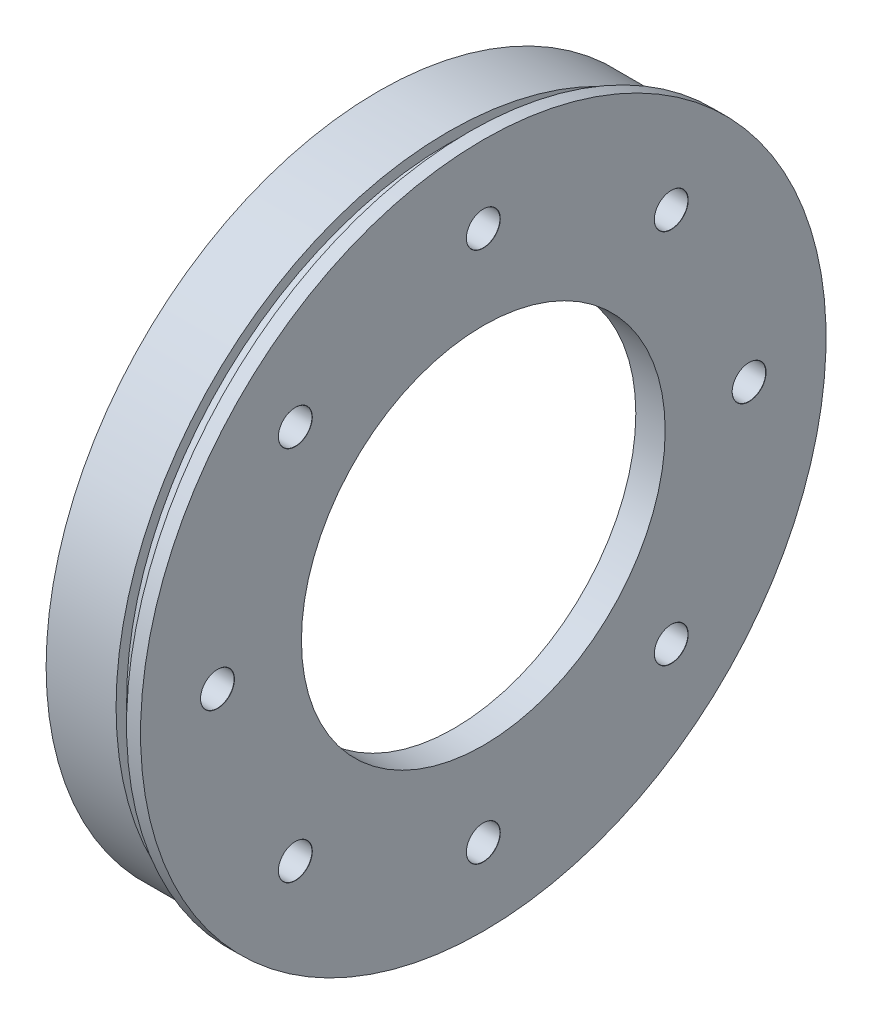
SolidWorks part; units mm, degrees
material "1.4305 (X8CrNiS18-9)"
ref_plane "Ebene vorne" through (0, 0, 0) normal (0, 0, 1) x (1, 0, 0)
ref_plane "Ebene oben" through (0, 0, 0) normal (0, 1, 0) x (1, 0, 0)
ref_plane "Ebene rechts" through (0, 0, 0) normal (1, 0, 0) x (0, 0, -1)
sketch "Sketch1" plane through (0, 0, 0) normal (0, 0, 1) x (1, 0, 0)
  line L0 (0, 0) -> (-24.3345, 0) construction
  line L1 (-15, 47.5) -> (-5, 47.5)
  line L2 (-5, 47.5) -> (-5, 46)
  line L3 (-5, 46) -> (-2, 46)
  line L4 (-2, 46) -> (-2, 49)
  line L5 (-2, 49) -> (0, 49)
  line L6 (0, 49) -> (0, 26)
  line L7 (0, 26) -> (-5, 26)
  line L8 (-5, 26) -> (-5, 42.8)
  line L9 (-5, 42.8) -> (-15, 42.8)
  line L10 (-15, 42.8) -> (-15, 47.5)
  point P12 (0, 0)
  dimension "D1" = 5
  dimension "D2" = 49
  dimension "D3" = 47.5
  dimension "D4" = 2
  dimension "D5" = 10
  dimension "D6" = 3
  dimension "D7" = 26
  dimension "D8" = 42.8
  dimension "D9" = 1.5
revolve "Revolve1" add sketch "Sketch1" angle 360 about L0
hole_wizard "M4 Clearance Hole1" positions "Sketch2" profile "Sketch3" hole size "M4" standard "DIN"
sketch "Sketch2" plane through (0, 0, 0) normal (1, 0, 0) x (0, 0, -1)
  point P0 (-38, 0)
  dimension "D1" = 38
sketch "Sketch3" plane through (0, 0, 38) normal (0, 1, 0) x (0, 0, -1)
  line L0 (0, 0) -> (0, 22.4421)
  line L1 (0, 22.4421) -> (2.4, 21)
  line L2 (2.4, 21) -> (2.4, 0.025)
  line L3 (2.4, 0.025) -> (2.425, 0)
  line L5 (2.425, 0) -> (0, 0)
  line L6 (-2.4, 0.025) -> (-2.425, 0) construction
  line L10 (0, 22.4421) -> (-2.4, 21) construction
  line L11 (0, -6.35) -> (0, 107.95) construction
  dimension "Hole Dia." = 4.8
  dimension "Hole Depth" = 21
  dimension "Near C'Sink Dia." = 4.85
  dimension "Near C'Sink Angle" = 90
  dimension "Drill Angle" = 118
pattern_circular "CirPattern1" count 8 over 360 about axis through (0, 0, 0) along (1, 0, 0) of "M4 Clearance Hole1"
sketch "Sketch4" plane through (-5, 0, 0) normal (-1, 0, 0) x (0, 0, 1)
  circle A0 centre (0, 0) radius 28
  circle A1 centre (0, 0) radius 26 construction
  dimension "D1" = 2
extrude "Cut-Extrude1" cut sketch "Sketch4" against normal blind 0.8
